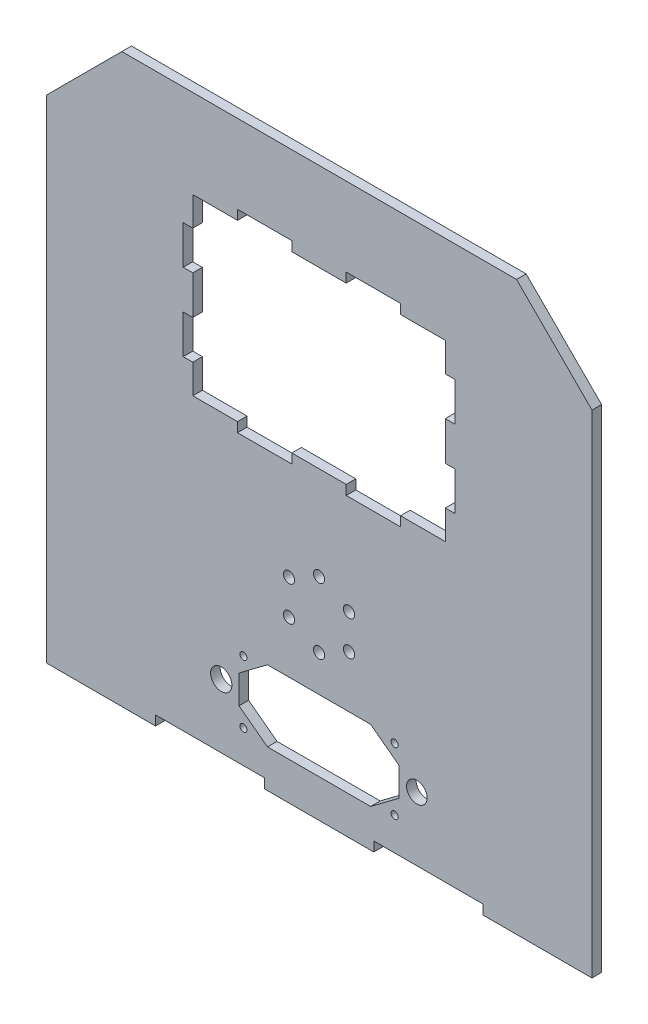
SolidWorks part; units mm, degrees
ref_plane "Ön Düzlem" through (0, 0, 0) normal (0, 0, 1) x (1, 0, 0)
ref_plane "Üst Düzlem" through (0, 0, 0) normal (0, 1, 0) x (1, 0, 0)
ref_plane "Sağ Düzlem" through (0, 0, 0) normal (1, 0, 0) x (0, 0, -1)
sketch "Sketch1" plane through (0, 0, 0) normal (0, 0, 1) x (1, 0, 0)
  line L21 (-45.9723, -28.1459) -> (-45.9723, -25.4459)
  line L22 (-15.2923, -28.1459) -> (-15.2923, -25.4459)
  line L23 (15.3877, -28.1459) -> (15.3877, -25.4459)
  line L24 (46.0677, -28.1459) -> (46.0677, -25.4459)
  line L26 (-76.6523, -23.1459) -> (-76.6523, 12.8541)
  line L27 (-76.6523, -23.1459) -> (-76.6523, -25.4459)
  line L28 (76.7477, -23.1459) -> (76.7477, 12.8541)
  line L30 (76.7477, -25.4459) -> (76.7477, -23.1459)
  line L33 (-45.9723, -28.1459) -> (-76.6523, -28.1459)
  line L34 (-76.6523, -28.1459) -> (-76.6523, -25.4459)
  line L35 (-15.2923, -25.4459) -> (-45.9723, -25.4459)
  line L36 (-15.2923, -28.1459) -> (15.3877, -28.1459)
  line L37 (15.3877, -25.4459) -> (46.0677, -25.4459)
  line L38 (46.0677, -28.1459) -> (76.7477, -28.1459)
  line L39 (76.7477, -28.1459) -> (76.7477, -25.4459)
  line L56 (-22.5, -3.5) -> (-14.5, 2.5)
  line L57 (-14.5, 2.5) -> (14.5, 2.5)
  line L58 (0, -17.5) -> (14.5, -17.5)
  line L59 (-14.5, -17.5) -> (-22.5, -11.5)
  line L60 (-22.5, -11.5) -> (-22.5, -3.5)
  line L61 (14.5, -17.5) -> (22.5, -11.5)
  line L62 (14.5, 2.5) -> (22.5, -3.5)
  line L63 (0, -17.5) -> (-14.5, -17.5)
  line L64 (22.5, -3.5) -> (22.5, -11.5)
  line L65 (35.5, 57.5) -> (22.92, 57.5)
  line L66 (35.5, 57.5) -> (35.5, 65.68)
  line L67 (35.5, 106.5) -> (22.92, 106.5)
  line L68 (-35.5, 57.5) -> (-35.5, 65.68)
  line L84 (-22.92, 54.8) -> (-7.64, 54.8)
  line L85 (-22.92, 109.2) -> (-7.64, 109.2)
  line L88 (38.2, 65.68) -> (38.2, 76.56)
  line L89 (7.64, 109.2) -> (22.92, 109.2)
  line L91 (-38.2, 65.68) -> (-38.2, 76.56)
  line L93 (-38.2, 87.44) -> (-38.2, 98.32)
  line L95 (-38.2, 98.32) -> (-35.5, 98.32)
  line L96 (-38.2, 87.44) -> (-35.5, 87.44)
  line L97 (-38.2, 76.56) -> (-35.5, 76.56)
  line L98 (-38.2, 65.68) -> (-35.5, 65.68)
  line L99 (35.5, 65.68) -> (38.2, 65.68)
  line L100 (35.5, 76.56) -> (38.2, 76.56)
  line L101 (35.5, 87.44) -> (38.2, 87.44)
  line L102 (35.5, 98.32) -> (38.2, 98.32)
  line L103 (-22.92, 109.2) -> (-22.92, 106.5)
  line L104 (-7.64, 109.2) -> (-7.64, 106.5)
  line L105 (7.64, 109.2) -> (7.64, 106.5)
  line L106 (22.92, 109.2) -> (22.92, 106.5)
  line L107 (-22.92, 57.5) -> (-22.92, 54.8)
  line L108 (-7.64, 57.5) -> (-7.64, 54.8)
  line L109 (7.64, 57.5) -> (7.64, 54.8)
  line L110 (22.92, 57.5) -> (22.92, 54.8)
  line L111 (-22.92, 106.5) -> (-35.5, 106.5)
  line L112 (7.64, 106.5) -> (-7.64, 106.5)
  line L113 (35.5, 98.32) -> (35.5, 106.5)
  line L114 (35.5, 76.56) -> (35.5, 87.44)
  line L115 (7.64, 57.5) -> (-7.64, 57.5)
  line L116 (-22.92, 57.5) -> (-35.5, 57.5)
  line L117 (-35.5, 76.56) -> (-35.5, 87.44)
  line L118 (-35.5, 98.32) -> (-35.5, 106.5)
  line L119 (38.2, 87.44) -> (38.2, 98.32)
  line L120 (7.64, 54.8) -> (22.92, 54.8)
  line L124 (-55.4391, 131.3541) -> (-76.6523, 110.1409)
  line L131 (55.5345, 131.3541) -> (76.7477, 110.1409)
  line L132 (76.7477, 12.8541) -> (76.7477, 110.1409)
  line L133 (-55.4391, 131.3541) -> (55.5345, 131.3541)
  line L134 (-76.6523, 12.8541) -> (-76.6523, 110.1409)
  circle A11 centre (-21.25, -16.25) radius 1
  circle A12 centre (-27.5, -7.5) radius 3
  circle A13 centre (-21.25, 1.25) radius 1
  circle A14 centre (21.25, -16.25) radius 1
  circle A15 centre (27.5, -7.5) radius 2.9
  circle A16 centre (21.25, 1.25) radius 1
  circle A17 centre (0, 31.25) radius 1.575
  circle A18 centre (0, 12.75) radius 1.575
  circle A19 centre (-8.4437, 17.125) radius 1.575
  circle A20 centre (-8.4437, 26.875) radius 1.575
  circle A21 centre (8.4437, 26.875) radius 1.575
  circle A22 centre (8.4437, 17.125) radius 1.575
  point P0 (0, 82)
  point P39 (0, 31.25)
  point P82 (0, 12.75)
extrude "Boss-Extrude3" add sketch "Sketch1" along normal blind 2.7
